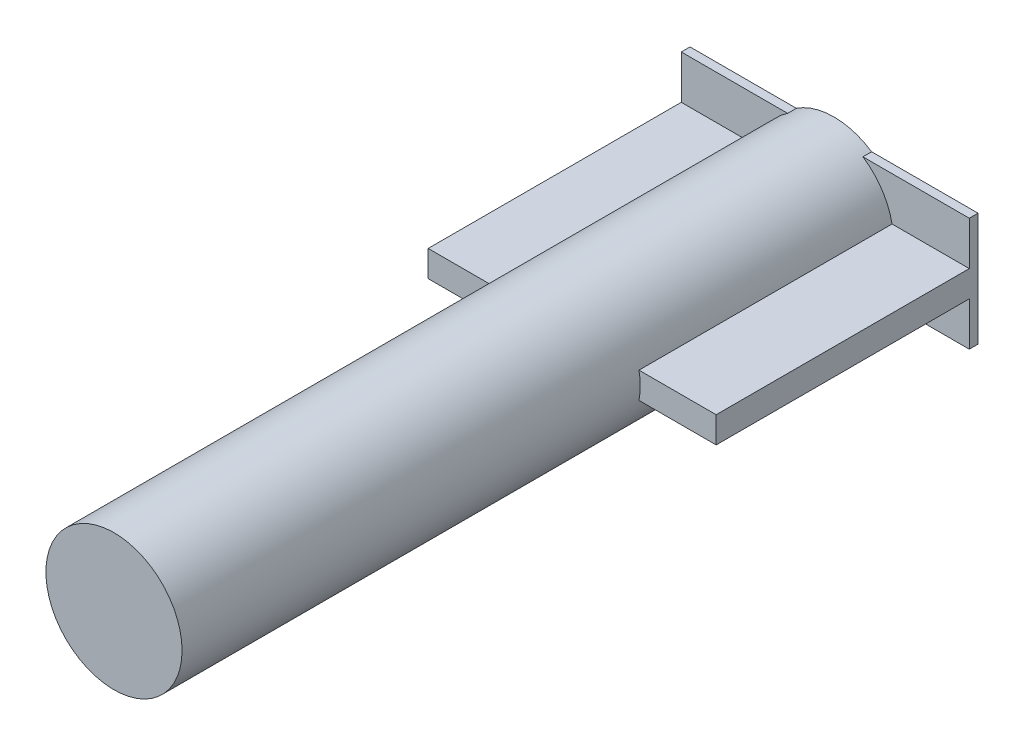
SolidWorks part; units mm, degrees
ref_plane "Front Plane" through (0, 0, 0) normal (0, 0, 1) x (1, 0, 0)
ref_plane "Top Plane" through (0, 0, 0) normal (0, 1, 0) x (1, 0, 0)
ref_plane "Right Plane" through (0, 0, 0) normal (1, 0, 0) x (0, 0, -1)
sketch "Sketch1" plane through (0, 0, 0) normal (0, 0, 1) x (1, 0, 0)
  circle A0 centre (0, 0) radius 7.8
  dimension "D1" = 15.6
extrude "Boss-Extrude1" add sketch "Sketch1" along normal blind 82.5
sketch "Sketch2" plane through (0, 0, 0) normal (0, 0, -1) x (-1, 0, 0)
  line L1 (-16.5, 6.5) -> (16.5, 6.5)
  line L2 (-16.5, 6.5) -> (-16.5, -6.5)
  line L3 (-16.5, -6.5) -> (16.5, -6.5)
  line L4 (16.5, 6.5) -> (16.5, -6.5)
  line L5 (-16.5, 6.5) -> (16.5, -6.5) construction
  line L6 (-16.5, -6.5) -> (16.5, 6.5) construction
  point P0 (0, 0)
  dimension "D1" = 13
  dimension "D2" = 33
extrude "Boss-Extrude2" add sketch "Sketch2" against normal blind 1
sketch "Sketch3" plane through (0, 0, 0) normal (0, 0, -1) x (-1, 0, 0)
  line L0 (16.5, -6.5) -> (16.5, 6.5) construction
  line L1 (-16.5, 1.5) -> (16.5, 1.5)
  line L2 (-16.5, 1.5) -> (-16.5, -1.5)
  line L3 (-16.5, -1.5) -> (16.5, -1.5)
  line L4 (16.5, 1.5) -> (16.5, -1.5)
  line L5 (-16.5, 1.5) -> (16.5, -1.5) construction
  line L6 (-16.5, -1.5) -> (16.5, 1.5) construction
  point P0 (0, 0)
  dimension "D1" = 3
extrude "Boss-Extrude3" add sketch "Sketch3" against normal blind 30
